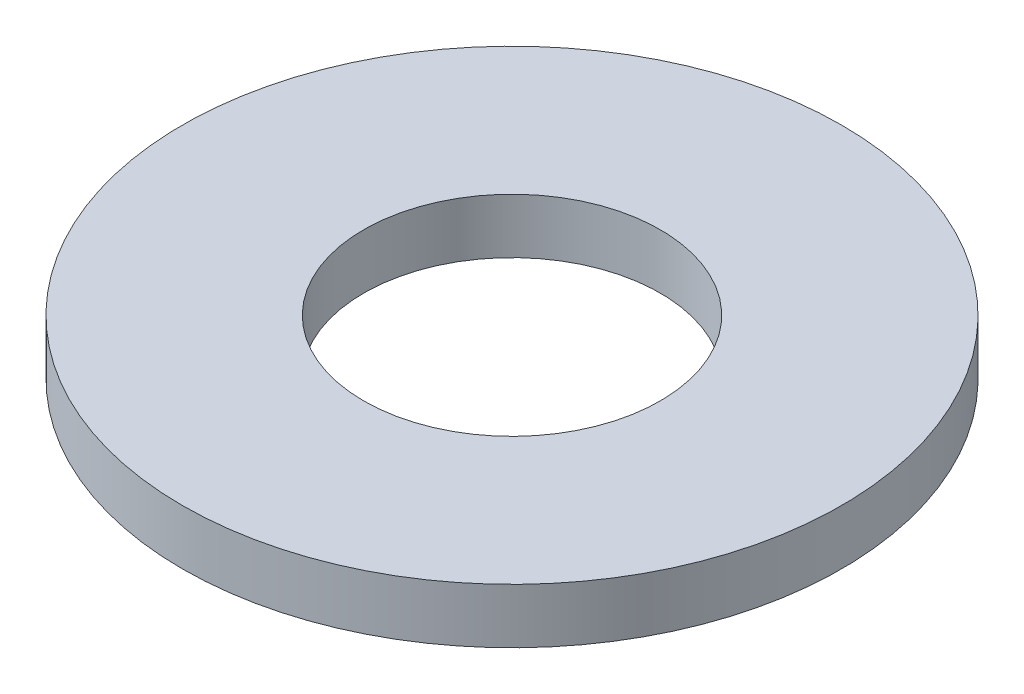
SolidWorks part; units mm, degrees
ref_plane "Front Plane" through (0, 0, 0) normal (0, 0, 1) x (1, 0, 0)
ref_plane "Top Plane" through (0, 0, 0) normal (0, 1, 0) x (1, 0, 0)
ref_plane "Right Plane" through (0, 0, 0) normal (1, 0, 0) x (0, 0, -1)
sketch "Sketch1" plane through (0, 0, 0) normal (0, 1, 0) x (1, 0, 0)
  circle A0 centre (0, 0) radius 4.05
  circle A1 centre (0, 0) radius 9
  dimension "D1" = 8.1
  dimension "D2" = 18
extrude "Boss-Extrude1" add sketch "Sketch1" along normal blind 1.5
